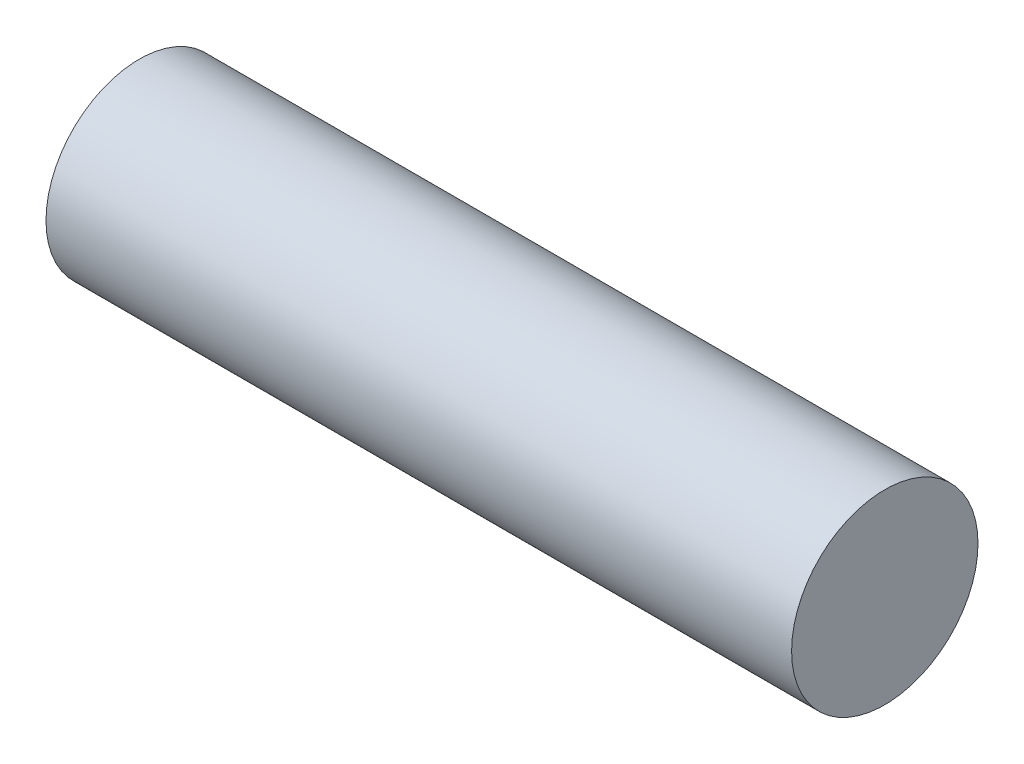
SolidWorks part; units mm, degrees
ref_plane "Front Plane" through (0, 0, 0) normal (0, 0, 1) x (1, 0, 0)
ref_plane "Top Plane" through (0, 0, 0) normal (0, 1, 0) x (1, 0, 0)
ref_plane "Right Plane" through (0, 0, 0) normal (1, 0, 0) x (0, 0, -1)
sketch "Sketch1" plane through (0, 0, 0) normal (1, 0, 0) x (0, 0, -1)
  circle A0 centre (0, 0) radius 6.35
  dimension "D1" = 12.7
extrude "Boss-Extrude1" add sketch "Sketch1" along normal blind 50.8
